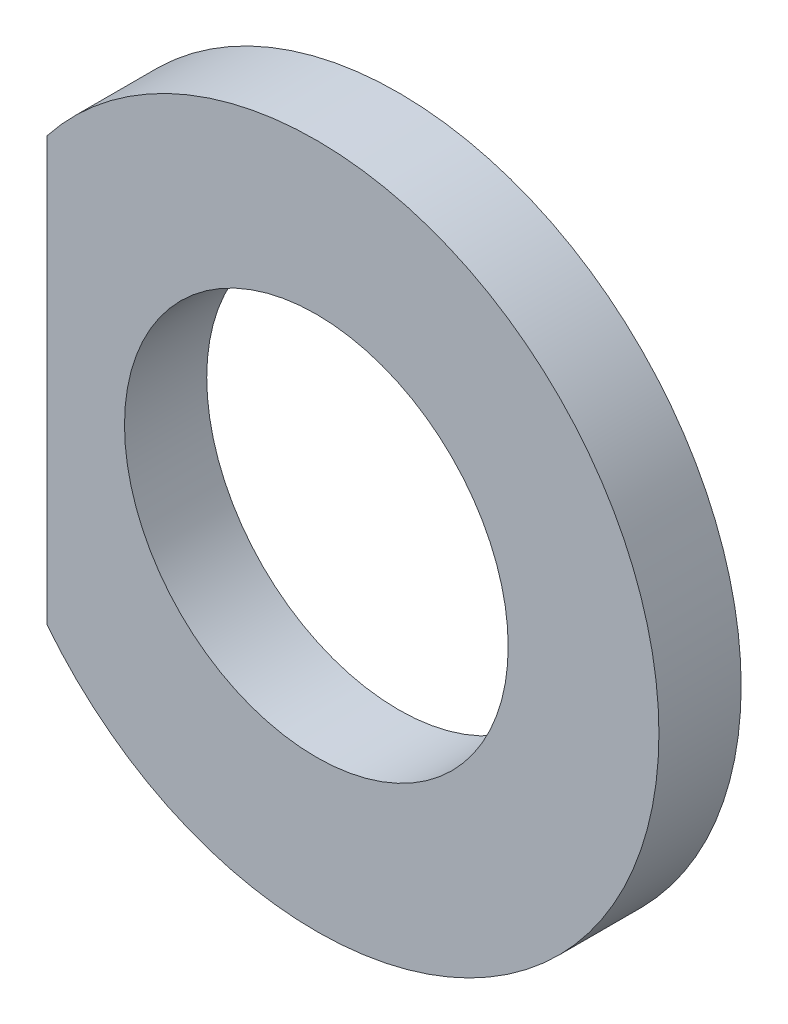
SolidWorks part; units mm, degrees
ref_plane "Front Plane" through (0, 0, 0) normal (0, 0, 1) x (1, 0, 0)
ref_plane "Top Plane" through (0, 0, 0) normal (0, 1, 0) x (1, 0, 0)
ref_plane "Right Plane" through (0, 0, 0) normal (1, 0, 0) x (0, 0, -1)
sketch "Sketch1" plane through (0, 0, 0) normal (0, 0, 1) x (1, 0, 0)
  line L0 (-5.9, 4.6303) -> (-5.9, -4.6303)
  line L1 (0, -7.5) -> (0, 7.5) construction
  line L2 (-4.2, 0) -> (4.2, 0) construction
  circle A0 centre (0, 0) radius 4.2
  arc A1 (-5.9, -4.6303) -> (-5.9, 4.6303) centre (0, 0) ccw
  point P10 (4.2, 0)
  dimension "ID" = 8.4
  dimension "OD" = 15
  dimension "B" = 13.4
extrude "Extrude1" add sketch "Sketch1" against normal blind 1.8
